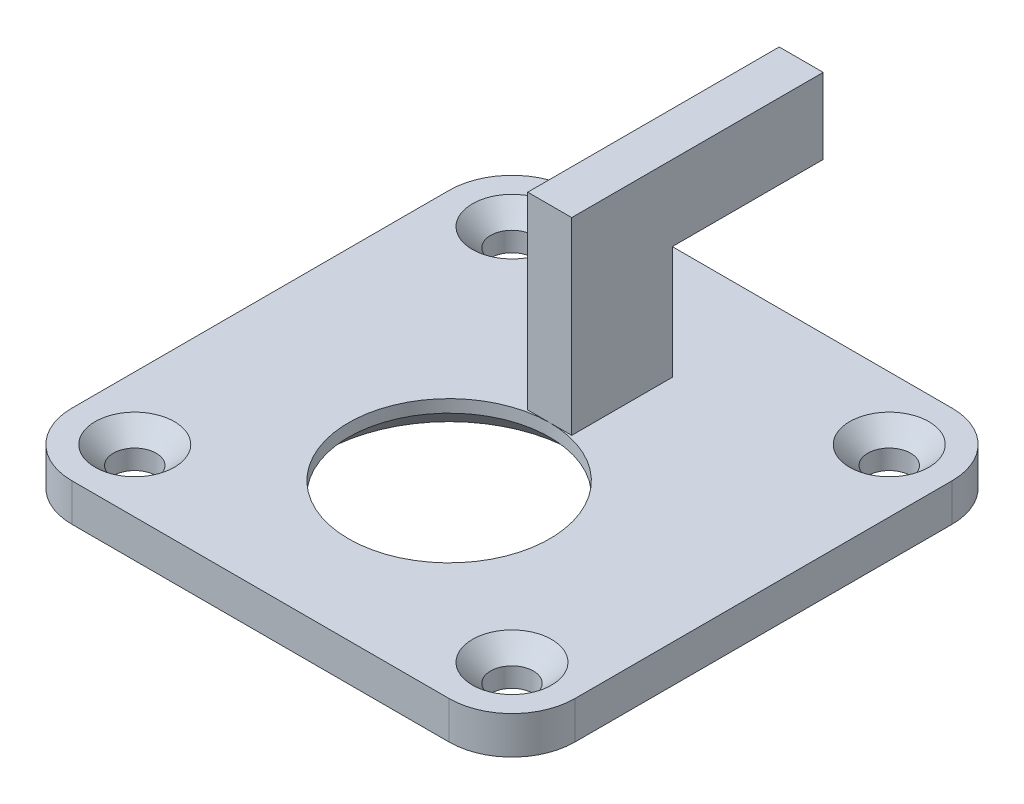
SolidWorks part; units mm, degrees
ref_plane "Front Plane" through (0, 0, 0) normal (0, 0, 1) x (1, 0, 0)
ref_plane "Top Plane" through (0, 0, 0) normal (0, 1, 0) x (1, 0, 0)
ref_plane "Right Plane" through (0, 0, 0) normal (1, 0, 0) x (0, 0, -1)
sketch "Sketch1" plane through (0, 0, 0) normal (0, 1, 0) x (1, 0, 0)
  line L0 (0, 0) -> (0, -15) construction
  line L1 (-15, -15) -> (15, -15)
  line L2 (-20, -10) -> (-20, 20)
  line L3 (-15, 25) -> (15, 25)
  line L4 (20, -10) -> (20, 20)
  circle A0 centre (0, 0) radius 8
  arc A1 (20, 20) -> (15, 25) centre (15, 20) ccw
  arc A2 (-15, 25) -> (-20, 20) centre (-15, 20) ccw
  arc A3 (20, -10) -> (15, -15) centre (15, -10) cw
  arc A4 (-15, -15) -> (-20, -10) centre (-15, -10) cw
  dimension "D1" = 16
  dimension "D4" = 5
  dimension "D5" = 5
  dimension "D2" = 15
  dimension "D3" = 40
  dimension "D6" = 25
extrude "Boss-Extrude1" add sketch "Sketch1" against normal blind 3
ref_point "Point1"
ref_point "Point2"
ref_point "Point3"
ref_point "Point4"
hole_wizard "CSK for M3 Countersunk Flat Head Screw1" positions "Sketch5" profile "Sketch6" countersink size "M3" standard "DIN" end condition through all
sketch "Sketch5" plane through (0, 0, 0) normal (0, 1, 0) x (1, 0, 0)
  point P0 (-15, 20)
  point P3 (15, 20)
  point P6 (15, -10)
  point P9 (-15, -10)
sketch "Sketch6" plane through (-15, 0, -20) normal (1, 0, 0) x (0, 0, 1)
  line L0 (0, 0) -> (0, 3)
  line L1 (0, 3) -> (1.7, 3)
  line L2 (1.7, 3) -> (1.7, 1.45)
  line L3 (1.7, 1.45) -> (3.15, 0)
  line L5 (3.15, 0) -> (0, 0)
  line L6 (-1.7, 1.45) -> (-3.15, 0) construction
  line L11 (0, -6.35) -> (0, 107.95) construction
  dimension "Thru Hole Dia." = 3.4
  dimension "Thru Hole Depth" = 3
  dimension "Near C'Sink Dia." = 6.3
  dimension "Near C'Sink Angle" = 90
chamfer "Chamfer1" distance 2 angle 45 1 edges at (0, -3, 8)
sketch "Sketch9" plane through (0, 0, 0) normal (1, 0, 0) x (0, 0, -1)
  line L0 (8, 0) -> (8, 15)
  line L1 (8, 15) -> (28, 15)
  line L2 (28, 15) -> (28, 9)
  line L3 (28, 9) -> (16, 9)
  line L4 (16, 9) -> (16, 0)
  line L5 (16, 0) -> (8, 0)
  line L7 (-10, 0) -> (20, 0) construction
  point P2 (15.3813, -0.311)
  dimension "D1" = 8
  dimension "D2" = 6
  dimension "D3" = 15
  dimension "D4" = 20
  dimension "D5" = 0
extrude "Boss-Extrude2" add sketch "Sketch9" along normal mid plane 3.5
